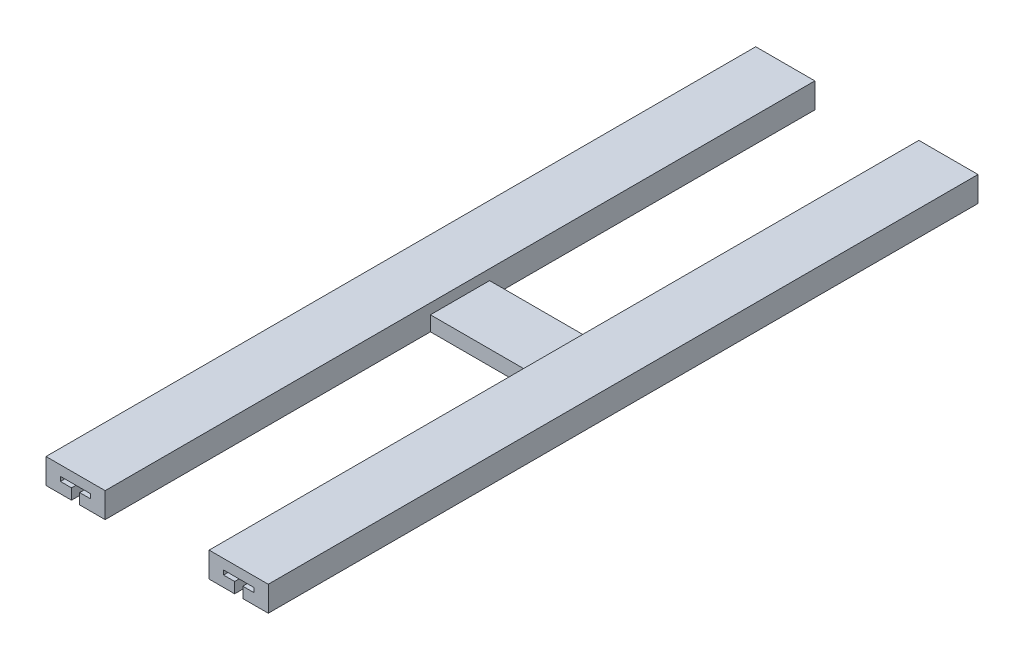
SolidWorks part; units mm, degrees
ref_plane "Front Plane" through (0, 0, 0) normal (0, 0, 1) x (1, 0, 0)
ref_plane "Top Plane" through (0, 0, 0) normal (0, 1, 0) x (1, 0, 0)
ref_plane "Right Plane" through (0, 0, 0) normal (1, 0, 0) x (0, 0, -1)
sketch "Sketch1" plane through (0, 0, 0) normal (0, 1, 0) x (1, 0, 0)
  line L0 (40, 489.6681) -> (40, 269.6681)
  line L1 (0, 489.6681) -> (40, 489.6681)
  line L2 (0, 9.6681) -> (0, 489.6681)
  line L3 (0, 9.6681) -> (40, 9.6681)
  line L4 (150, 10) -> (150, 490)
  line L5 (110, 490) -> (110, 269.6681)
  line L6 (110, 490) -> (150, 490)
  line L7 (110, 10) -> (150, 10)
  line L8 (40, 269.6681) -> (110, 269.6681)
  line L9 (40, 229.6681) -> (110, 229.6681)
  line L10 (0, 249.6681) -> (279.0452, 249.6681) construction
  line L11 (40, 229.6681) -> (40, 9.6681)
  line L12 (110, 229.6681) -> (110, 10)
  dimension "D1" = 480
  dimension "D2" = 480
  dimension "D3" = 40
  dimension "D4" = 40
  dimension "D5" = 40
extrude "Boss-Extrude1" add sketch "Sketch1" along normal blind 17
sketch "Sketch2" plane through (0, 17, 0) normal (0, 1, 0) x (1, 0, 0)
  line L1 (40, 269.6681) -> (110, 269.6681)
  line L2 (40, 269.6681) -> (40, 229.6681)
  line L3 (40, 229.6681) -> (110, 229.6681)
  line L4 (110, 269.6681) -> (110, 229.6681)
extrude "Cut-Extrude1" cut sketch "Sketch2" against normal blind 7
sketch "Sketch3" plane through (0, 0, -9.6681) normal (0, 0, 1) x (1, 0, 0)
  line L0 (20, 0) -> (20, 20.682) construction
  line L1 (0, 0) -> (40, 0) construction
  line L2 (17.25, 0) -> (17.25, 7.25)
  line L3 (17.25, 7.25) -> (9.75, 7.25)
  line L4 (9.75, 7.25) -> (9.75, 10.25)
  line L5 (9.75, 10.25) -> (30.25, 10.25)
  line L6 (30.25, 10.25) -> (30.25, 7.25)
  line L7 (30.25, 7.25) -> (22.75, 7.25)
  line L8 (22.75, 7.25) -> (22.75, 0)
  line L9 (22.75, 0) -> (17.25, 0)
  line L10 (9.75, 8.75) -> (36.0403, 8.75) construction
  dimension "D1" = 20.5
  dimension "D2" = 3
  dimension "D3" = 5.5
  dimension "D4" = 10.25
extrude "Cut-Extrude2" cut sketch "Sketch3" against normal through all
ref_plane "Plane1" through (75, 0, 0) normal (1, 0, 0) x (0, 0, -1)
mirror "Mirror1" about plane through (75, 0, 0) normal (1, 0, 0) of "Cut-Extrude2"
